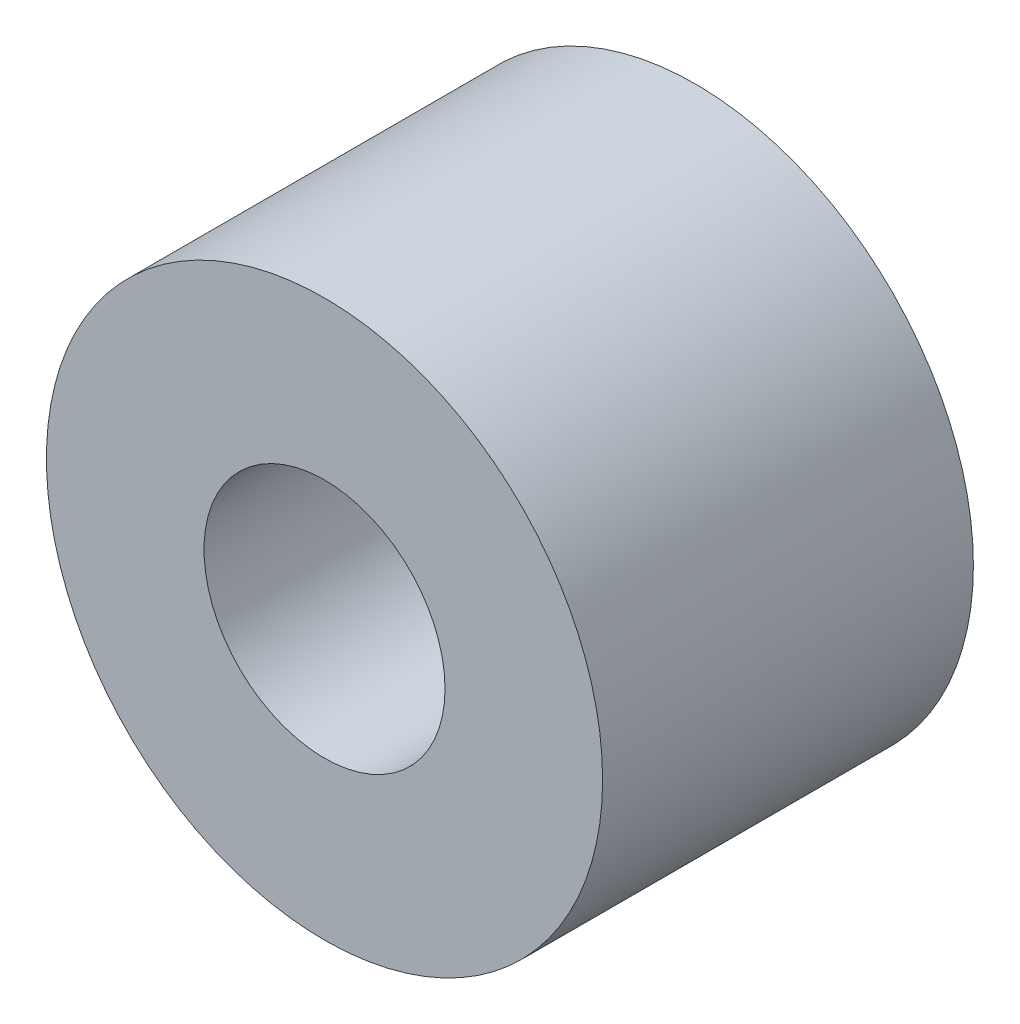
SolidWorks part; units mm, degrees
material "PE High Density"
ref_plane "Front Plane" through (0, 0, 0) normal (0, 0, 1) x (1, 0, 0)
ref_plane "Top Plane" through (0, 0, 0) normal (0, 1, 0) x (1, 0, 0)
ref_plane "Right Plane" through (0, 0, 0) normal (1, 0, 0) x (0, 0, -1)
sketch "Sketch1" plane through (0, 0, 0) normal (0, 0, 1) x (1, 0, 0)
  circle A0 centre (0, 0) radius 9.525 construction
  circle A1 centre (0, 0) radius 4.1275 construction
  point P4 (0, 9.525)
  dimension "OD" = 19.05
  dimension "ID" = 8.255
sketch "Sketch2" plane through (0, 0, 0) normal (1, 0, 0) x (0, 0, -1)
  line L0 (-6.35, 9.525) -> (6.35, 9.525) construction
  dimension "Length" = 12.7
sketch "Sketch3" plane through (0, 0, 0) normal (0, 0, 1) x (1, 0, 0)
  circle A0 centre (0, 0) radius 4.1275 construction
  circle A1 centre (0, 0) radius 9.525 construction
  circle A2 centre (0, 0) radius 4.1275
  circle A3 centre (0, 0) radius 9.525
extrude "Boss-Extrude1" add sketch "Sketch3" against normal up to vertex (6.35 mm away) and the other way up to vertex (6.35 mm away) up to point (0, 9.525, -6.35) other way up to point (0, 9.525, 6.35)
